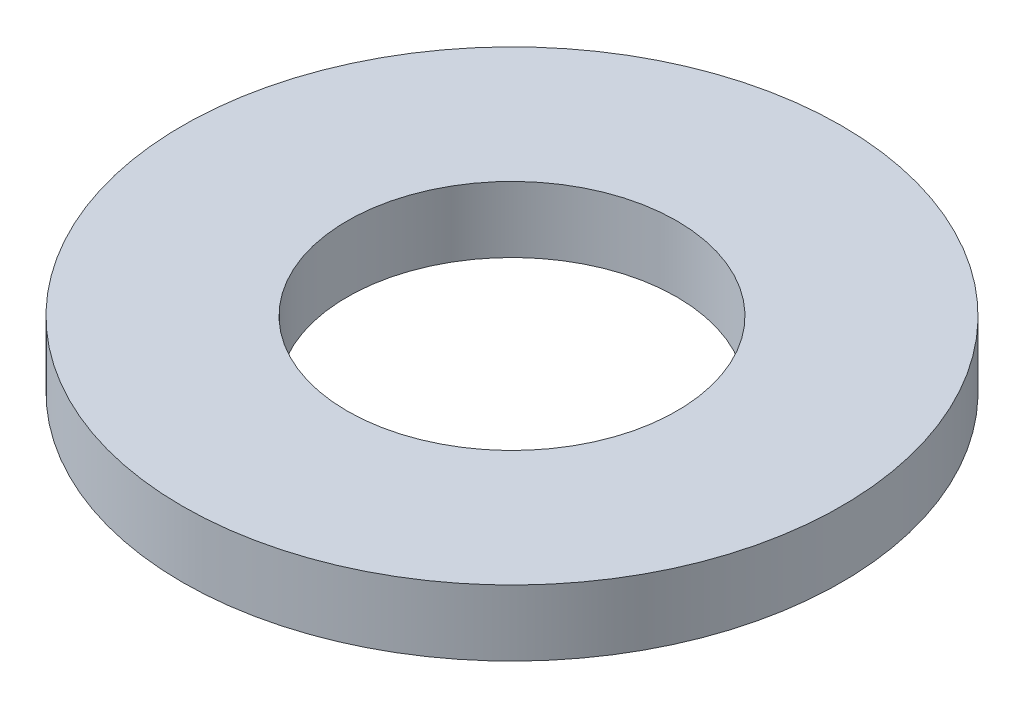
SolidWorks part; units mm, degrees
material "AISI Type 316L stainless steel"
ref_plane "Front Plane" through (0, 0, 0) normal (0, 0, 1) x (1, 0, 0)
ref_plane "Top Plane" through (0, 0, 0) normal (0, 1, 0) x (1, 0, 0)
ref_plane "Right Plane" through (0, 0, 0) normal (1, 0, 0) x (0, 0, -1)
sketch "Sketch1" plane through (0, 0, 0) normal (0, 1, 0) x (1, 0, 0)
  circle A0 centre (0, 0) radius 2.5
  circle A1 centre (0, 0) radius 5
  dimension "D1" = 5
  dimension "D2" = 10
extrude "Boss-Extrude1" add sketch "Sketch1" along normal mid plane 1
